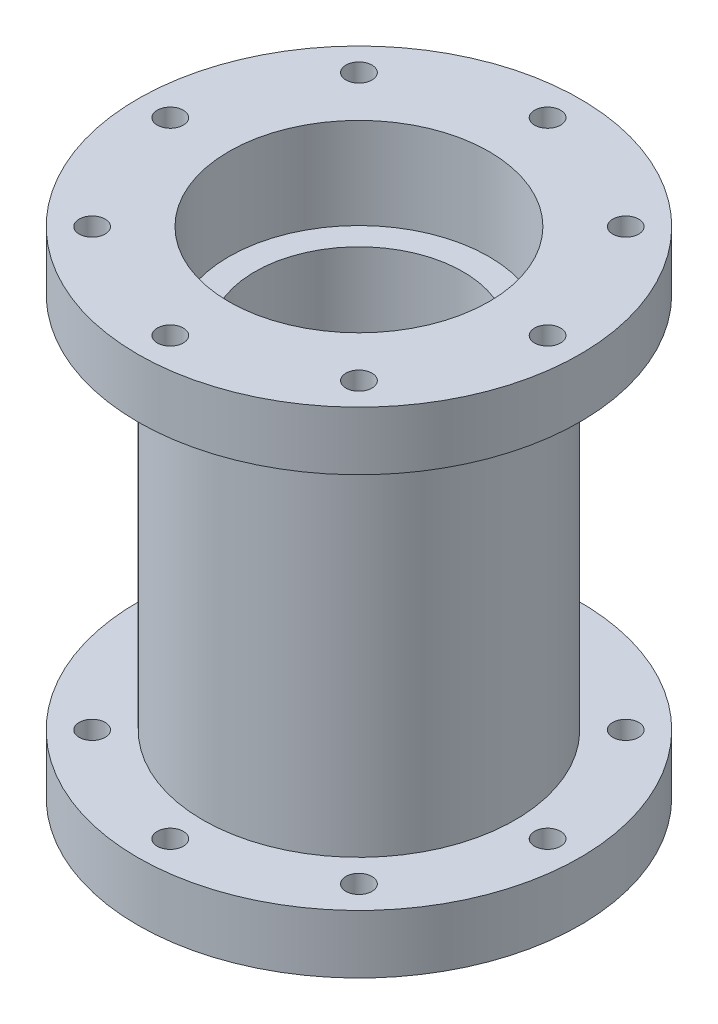
SolidWorks part; units mm, degrees
other "Markup1"
sketch "Sketch3" plane through (21.5, 17.5, -21.5) normal (0.4427, 0.8962, -0.0285) x (0.8481, -0.4288, -0.3112)
material "6061-T4 (SS)"
ref_plane "Front Plane" through (0, 0, 0) normal (0, 0, 1) x (1, 0, 0)
ref_plane "Top Plane" through (0, 0, 0) normal (0, 1, 0) x (1, 0, 0)
ref_plane "Right Plane" through (0, 0, 0) normal (1, 0, 0) x (0, 0, -1)
sketch "Sketch1" plane through (0, 0, 0) normal (0, 0, 1) x (1, 0, 0)
  line L0 (0, 75.0968) -> (0, -85.1516) construction
  line L1 (-12, 8) -> (-12, -8)
  line L2 (-12, -8) -> (-16, -8)
  line L3 (-16, -8) -> (-16, -24)
  line L4 (-16, -24) -> (-20, -24)
  line L5 (-20, -24) -> (-20, -38)
  line L13 (-24, 38) -> (-24, -38)
  line L14 (-12, 0) -> (48.9465, 0) construction
  line L15 (-20, 24) -> (-20, 38)
  line L16 (-16, 24) -> (-20, 24)
  line L17 (-16, 8) -> (-16, 24)
  line L18 (-12, 8) -> (-16, 8)
  line L19 (-24, 38) -> (-20, 38)
  line L20 (-24, -38) -> (-20, -38)
  line L21 (-12, 0) -> (-64.4373, 0) construction
  point P18 (0, 0)
  dimension "D2" = 16
  dimension "D3" = 20
  dimension "D4" = 12
  dimension "D5" = 16
  dimension "D1" = 4
  dimension "D6" = 14
  dimension "D7" = 16
revolve "Revolve1" add sketch "Sketch1" angle 360 about L0
sketch "Sketch4" plane through (0, 38, 0) normal (0, 1, 0) x (1, 0, 0)
  circle A0 centre (0, 0) radius 24
  circle A1 centre (0, 0) radius 34
  circle A2 centre (0, 0) radius 29 construction
  circle A3 centre (0, 29) radius 2
  circle A4 centre (20.5061, 20.5061) radius 2
  circle A5 centre (29, 0) radius 2
  circle A6 centre (20.5061, -20.5061) radius 2
  circle A7 centre (0, -29) radius 2
  circle A8 centre (-20.5061, -20.5061) radius 2
  circle A9 centre (-29, 0) radius 2
  circle A10 centre (-20.5061, 20.5061) radius 2
  point P16 (0, 0)
  dimension "D1" = 48
  dimension "D2" = 10
  dimension "D3" = 58
  dimension "D4" = 4
  dimension "D5" = 8
extrude "Boss-Extrude1" add sketch "Sketch4" against normal blind 9
mirror "Mirror1" about plane through (0, 0, 0) normal (0, 1, 0) of "Boss-Extrude1"
